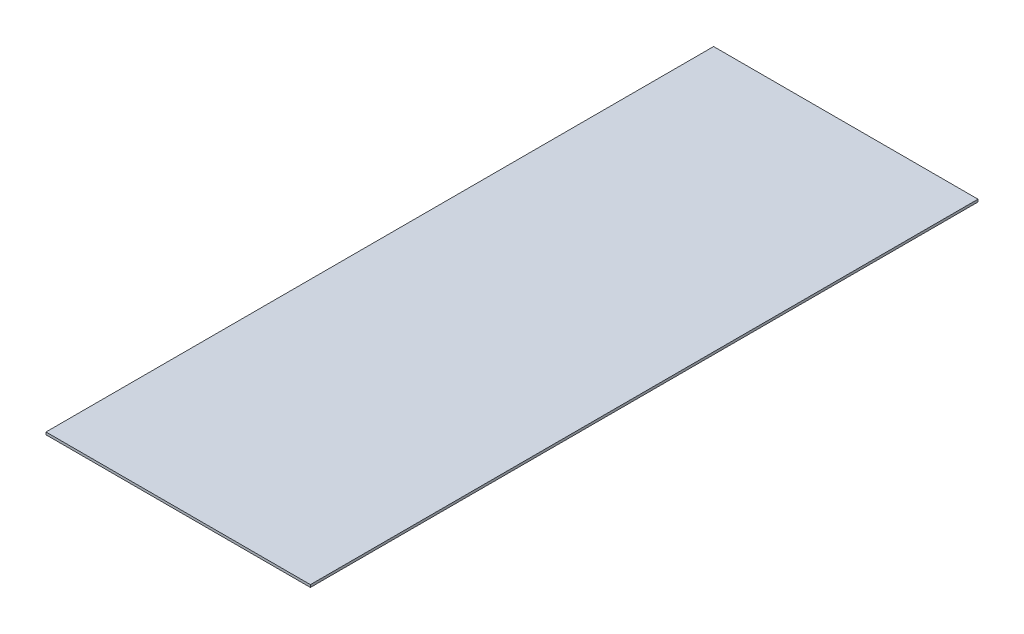
SolidWorks part; units mm, degrees
material "Hexcel AS4C (3000 Filaments)"
ref_plane "Front Plane" through (0, 0, 0) normal (0, 0, 1) x (1, 0, 0)
ref_plane "Top Plane" through (0, 0, 0) normal (0, 1, 0) x (1, 0, 0)
ref_plane "Right Plane" through (0, 0, 0) normal (1, 0, 0) x (0, 0, -1)
sketch "Sketch1" plane through (0, 0, 0.0479) normal (0, 1, 0) x (1, 0, 0)
  line L1 (-32.2125, 199.9208) -> (127.7875, 199.9208)
  line L2 (-32.2125, 199.9208) -> (-32.2125, -204.0792)
  line L3 (-32.2125, -204.0792) -> (127.7875, -204.0792)
  line L4 (127.7875, 199.9208) -> (127.7875, -204.0792)
  dimension "D1" = 160
  dimension "D2" = 404
extrude "Boss-Extrude1" add sketch "Sketch1" along normal blind 1.5
ref_plane "Plane1" through (0, 1.5, 0) normal (0, 1, 0) x (1, 0, 0)
sketch "Sketch2" plane through (0, 1.5, 0) normal (0, 1, 0) x (1, 0, 0)
  line L0 (-32.2125, -204.1271) -> (47.7875, -204.1271)
  line L1 (-32.2125, -204.1271) -> (127.7875, -204.1271) construction
  line L2 (47.7875, -204.1271) -> (47.7875, 199.8729)
  line L3 (127.7875, 199.8729) -> (-32.2125, 199.8729) construction
  line L5 (32.7875, 202) -> (62.7875, 202)
  line L6 (32.7875, 202) -> (32.7875, -202)
  line L7 (32.7875, -202) -> (62.7875, -202)
  line L8 (62.7875, 202) -> (62.7875, -202)
  line L9 (32.7875, 202) -> (62.7875, -202) construction
  line L10 (32.7875, -202) -> (62.7875, 202) construction
  point P5 (47.7875, 0)
  dimension "D1" = 30
  dimension "D2" = 404
